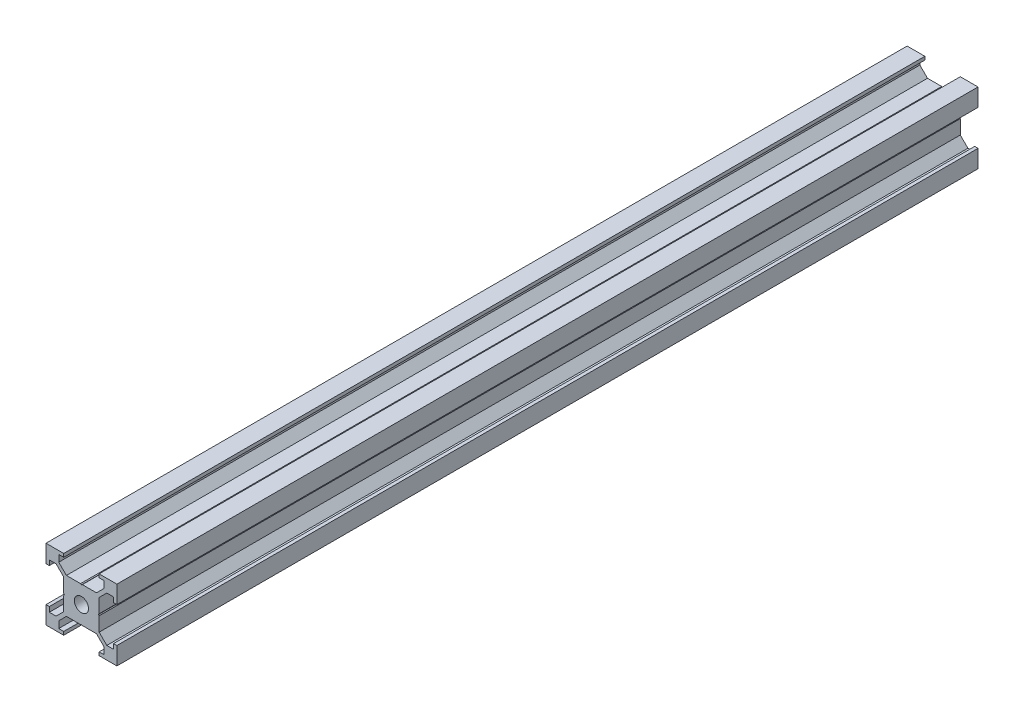
SolidWorks part; units mm, degrees
material "5052-H38"
ref_plane "Front Plane" through (0, 0, 0) normal (0, 0, 1) x (1, 0, 0)
ref_plane "Top Plane" through (0, 0, 0) normal (0, 1, 0) x (1, 0, 0)
ref_plane "Right Plane" through (0, 0, 0) normal (1, 0, 0) x (0, 0, -1)
sketch "Sketch1" plane through (0, 0, 0) normal (0, 0, 1) x (1, 0, 0)
  line L0 (-10, 5) -> (-9.0563, 5)
  line L1 (10, -10) -> (5, -10)
  line L2 (10, -10) -> (10, -5)
  line L3 (10, 10) -> (5, 10)
  line L4 (-10, -10) -> (-10, -5)
  line L5 (10, -10) -> (-10, 10) construction
  line L6 (10, 10) -> (-10, -10) construction
  line L7 (5, -5) -> (0.2457, -5)
  line L8 (5, -5) -> (5, -0.2457)
  line L9 (5, 5) -> (0.2457, 5)
  line L10 (-5, -5) -> (-5, -0.2457)
  line L11 (5, -5) -> (-5, 5) construction
  line L12 (5, 5) -> (-5, -5) construction
  line L13 (-9.0563, 5) -> (-9.0563, 6.4)
  line L14 (-9.0563, 6.4) -> (-7.1563, 6.4)
  line L15 (-7.1563, 6.4) -> (-5, 4.2437)
  line L16 (-5, 10) -> (-5, 9.0563)
  line L17 (-5, 9.0563) -> (-6.4, 9.0563)
  line L18 (-6.4, 9.0563) -> (-6.4, 7.1563)
  line L19 (-6.4, 7.1563) -> (-4.2437, 5)
  line L20 (5, 10) -> (5, 9.0563)
  line L21 (5, 9.0563) -> (6.4, 9.0563)
  line L22 (6.4, 9.0563) -> (6.4, 7.1563)
  line L23 (6.4, 7.1563) -> (4.2437, 5)
  line L24 (7.1563, 6.4) -> (5, 4.2437)
  line L25 (9.0563, 6.4) -> (7.1563, 6.4)
  line L26 (10, 5) -> (9.0563, 5)
  line L27 (9.0563, 5) -> (9.0563, 6.4)
  line L28 (10, -5) -> (9.0563, -5)
  line L29 (9.0563, -5) -> (9.0563, -6.4)
  line L30 (9.0563, -6.4) -> (7.1563, -6.4)
  line L31 (7.1563, -6.4) -> (5, -4.2437)
  line L32 (6.4, -7.1563) -> (4.2437, -5)
  line L33 (6.4, -9.0563) -> (6.4, -7.1563)
  line L34 (5, -10) -> (5, -9.0563)
  line L35 (5, -9.0563) -> (6.4, -9.0563)
  line L36 (-5, -10) -> (-5, -9.0563)
  line L37 (-5, -9.0563) -> (-6.4, -9.0563)
  line L38 (-6.4, -9.0563) -> (-6.4, -7.1563)
  line L39 (-6.4, -7.1563) -> (-4.2437, -5)
  line L40 (-7.1563, -6.4) -> (-5, -4.2437)
  line L41 (-9.0563, -6.4) -> (-7.1563, -6.4)
  line L42 (-10, -5) -> (-9.0563, -5)
  line L43 (-9.0563, -5) -> (-9.0563, -6.4)
  line L44 (0, 0) -> (-5, 0) construction
  line L45 (-5, 0.2457) -> (-4.8279, 0)
  line L46 (-4.8279, 0) -> (-5, -0.2457)
  line L47 (0.2457, 5) -> (0, 4.8279)
  line L48 (0, 4.8279) -> (-0.2457, 5)
  line L49 (5, -0.2457) -> (4.8279, 0)
  line L50 (4.8279, 0) -> (5, 0.2457)
  line L51 (-0.2457, -5) -> (0, -4.8279)
  line L52 (0, -4.8279) -> (0.2457, -5)
  line L53 (-0.2457, 5) -> (-5, 5)
  line L54 (5, 0.2457) -> (5, 5)
  line L55 (-0.2457, -5) -> (-5, -5)
  line L56 (-5, 0.2457) -> (-5, 5)
  line L57 (-10, 5) -> (-10, 10)
  line L58 (-5, 10) -> (-10, 10)
  line L59 (-5, -10) -> (-10, -10)
  line L60 (10, 5) -> (10, 10)
  circle A0 centre (0, 0) radius 2
  point P0 (0, 0)
  point P6 (0, 0)
  point P56 (0, 0)
  point P70 (0, 0)
  dimension "D10" = 4
  dimension "D1" = 20
  dimension "D2" = 10
  dimension "D3" = 1.4
  dimension "D4" = 1.9
  dimension "D5" = 3.0494
  dimension "D7" = 0.3
  dimension "D8" = 35
  dimension "D6" = 4
  dimension "D9" = 4
extrude "Boss-Extrude1" add sketch "Sketch1" along normal blind 243 contours L26 L60 L3 L20 L21 L22 L23 L9 L54 L24 L25 L27 | L56 L45 L46 L10 L55 L51 L52 L7 L8 L49 L50 L54 L9 L47 L48 L53 A0 | L16 L58 L57 L0 L13 L14 L15 L56 L53 L19 L18 L17 | L59 L36 L37 L38 L39 L55 L10 L40 L41 L43 L42 L4 | L35 L34 L1 L2 L28 L29 L30 L31 L8 L7 L32 L33
